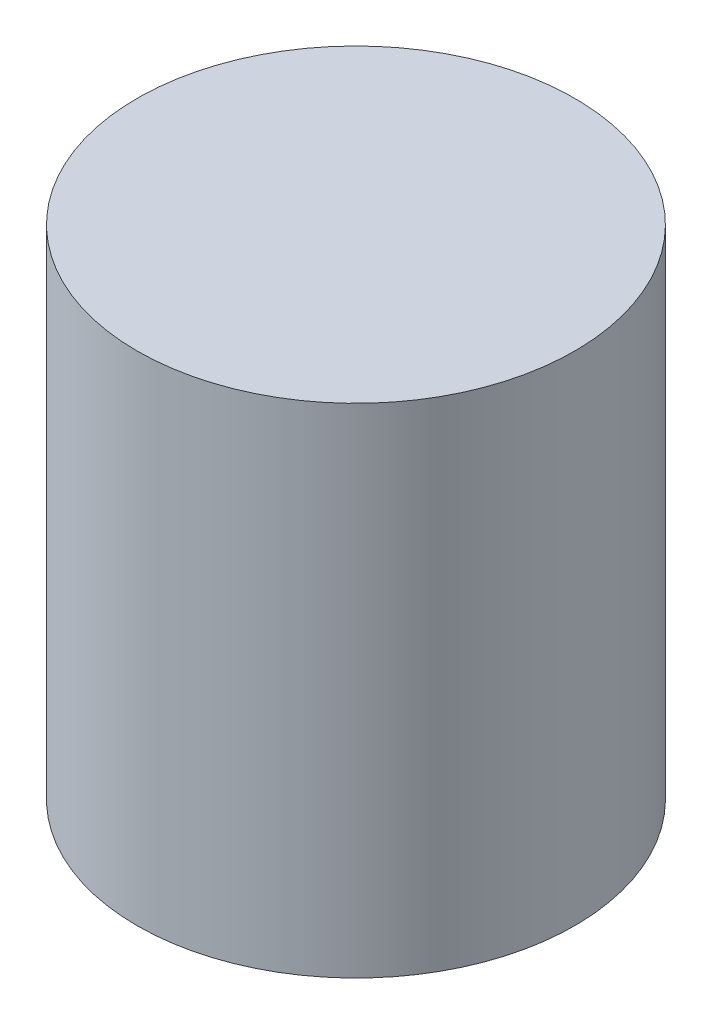
SolidWorks part; units mm, degrees
ref_plane "Front Plane" through (0, 0, 0) normal (0, 0, 1) x (1, 0, 0)
ref_plane "Top Plane" through (0, 0, 0) normal (0, 1, 0) x (1, 0, 0)
ref_plane "Right Plane" through (0, 0, 0) normal (1, 0, 0) x (0, 0, -1)
sketch "Sketch1" plane through (0, 0, 0) normal (0, 1, 0) x (1, 0, 0)
  circle A0 centre (0, 0) radius 25.5
  dimension "D1" = 51
extrude "Boss-Extrude1" add sketch "Sketch1" along normal blind 58
sketch "Sketch2" plane through (0, 0, 0) normal (0, -1, 0) x (1, 0, 0)
  circle A0 centre (0, 0) radius 22.5
  dimension "D1" = 45
extrude "Cut-Extrude1" cut sketch "Sketch2" against normal blind 55
